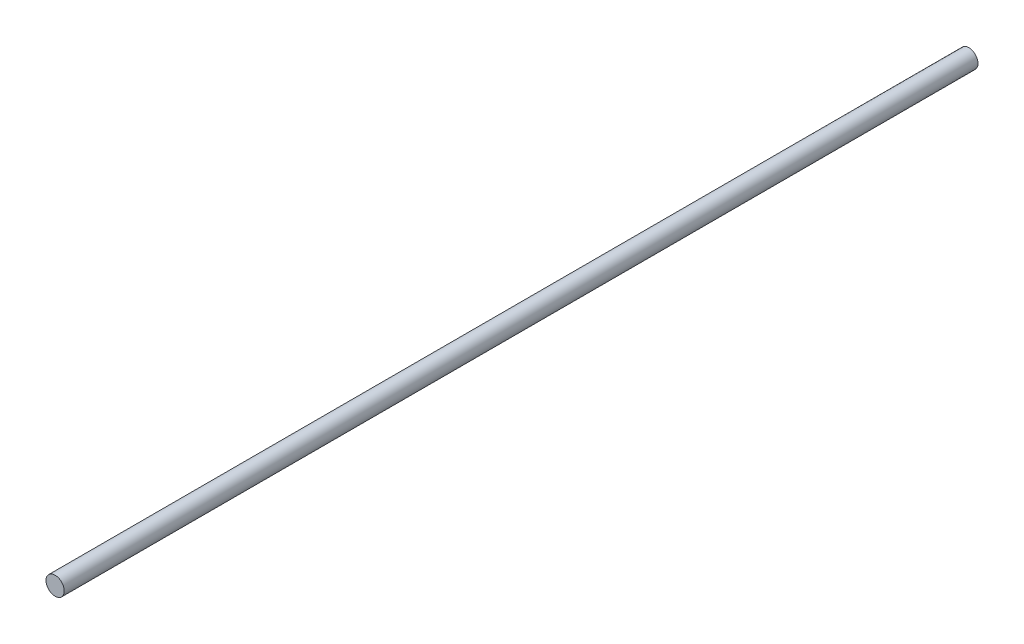
SolidWorks part; units mm, degrees
ref_plane "前视基准面" through (0, 0, 0) normal (0, 0, 1) x (1, 0, 0)
ref_plane "上视基准面" through (0, 0, 0) normal (0, 1, 0) x (1, 0, 0)
ref_plane "右视基准面" through (0, 0, 0) normal (1, 0, 0) x (0, 0, -1)
sketch "草图1" plane through (0, 0, 0) normal (0, 0, 1) x (1, 0, 0)
  circle A0 centre (0, 0) radius 4
  dimension "D1" = 8
extrude "凸台-拉伸1" add sketch "草图1" along normal blind 400
